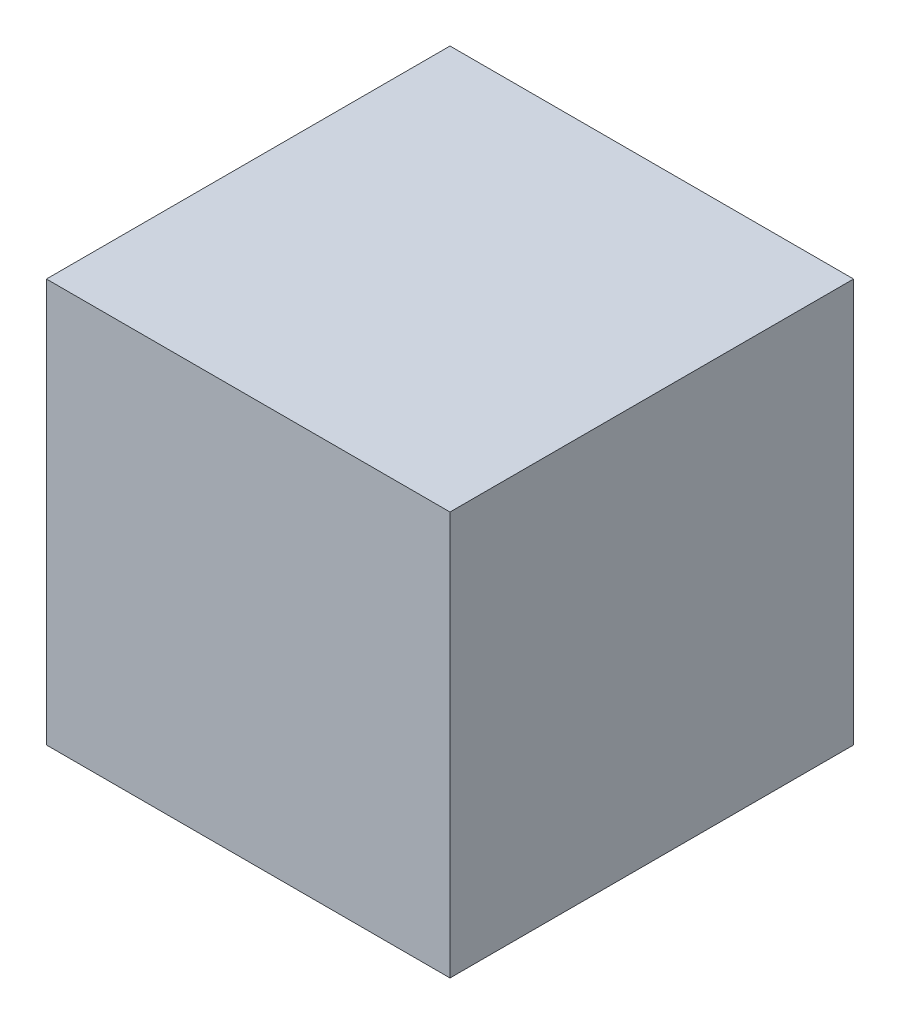
SolidWorks part; units mm, degrees
ref_plane "Front Plane" through (0, 0, 0) normal (0, 0, 1) x (1, 0, 0)
ref_plane "Top Plane" through (0, 0, 0) normal (0, 1, 0) x (1, 0, 0)
ref_plane "Right Plane" through (0, 0, 0) normal (1, 0, 0) x (0, 0, -1)
sketch "Sketch1" plane through (0, 0, 0) normal (0, 1, 0) x (1, 0, 0)
  line L1 (0, 0) -> (-139.7, 0)
  line L2 (0, 0) -> (0, 139.7)
  line L3 (0, 139.7) -> (-139.7, 139.7)
  line L4 (-139.7, 0) -> (-139.7, 139.7)
  dimension "D1" = 139.7
  dimension "D2" = 139.7
extrude "Boss-Extrude1" add sketch "Sketch1" along normal blind 139.7
